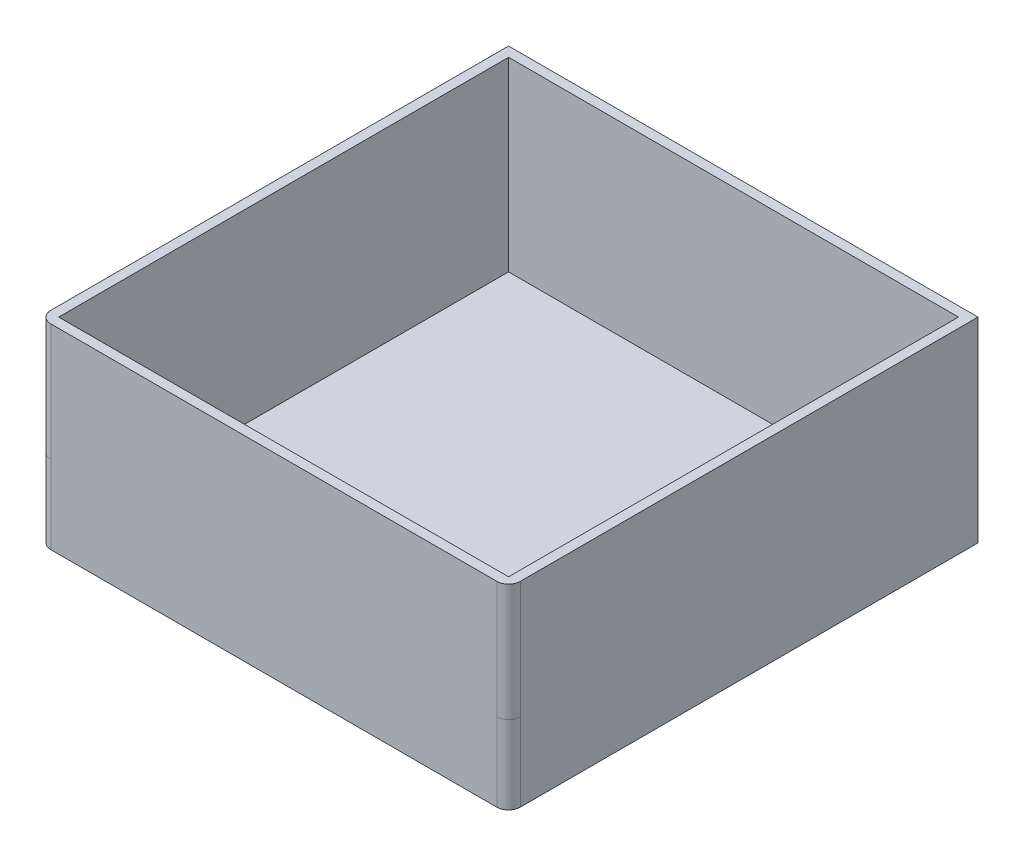
SolidWorks part; units mm, degrees
ref_plane "Plan de face" through (0, 0, 0) normal (0, 0, 1) x (1, 0, 0)
ref_plane "Plan de dessus" through (0, 0, 0) normal (0, 1, 0) x (1, 0, 0)
ref_plane "Plan de droite" through (0, 0, 0) normal (1, 0, 0) x (0, 0, -1)
sketch "Esquisse2" plane through (0, 0, 0) normal (1, 0, 0) x (0, 0, -1)
  line L0 (0, 0) -> (0, 20)
  line L1 (0, 20) -> (120, 20)
  line L2 (120, 20) -> (120, 0)
  line L3 (120, 0) -> (118.744, 0)
  line L4 (0, 0) -> (120, 0)
  dimension "D1" = 20
  dimension "D2" = 120
extrude "Boss.-Extru.1" add sketch "Esquisse2" along normal blind 120 contours L0 L4 L3 L2 L1
fillet "Congé1" radius 3 2 edges at (0, 10, 0) (120, 10, 0)
sketch "Esquisse3" plane through (0, 20, 0) normal (0, 1, 0) x (1, 0, 0)
  line L0 (0, 120) -> (120, 120) construction
  line L1 (120, 120) -> (60, 120) construction
  line L2 (60, 120) -> (60, 0) construction
  line L3 (117, 0) -> (3, 0) construction
  line L4 (60, 0) -> (60, 60) construction
  line L5 (60, 60) -> (0, 60) construction
  line L6 (0, 3) -> (0, 120) construction
  line L7 (0, 60) -> (120, 60) construction
  line L8 (120, 3) -> (120, 120) construction
  line L9 (120, 60) -> (60, 0) construction
  line L10 (60, 0) -> (0, 60) construction
  line L11 (0, 60) -> (60, 120) construction
  line L12 (60, 120) -> (120, 60) construction
  line L13 (60, 120) -> (60, 117.5) construction
  line L14 (120, 60) -> (117.5, 60) construction
  line L15 (60, 0) -> (60, 2.5) construction
  line L16 (0, 60) -> (2.5, 60) construction
  line L18 (60, 117.5) -> (117.5, 117.5)
  line L19 (60, 117.5) -> (60, 60)
  line L20 (60, 60) -> (117.5, 60)
  line L21 (117.5, 117.5) -> (117.5, 60)
  line L22 (117.5, 60) -> (60, 60)
  line L23 (117.5, 60) -> (117.5, 2.5)
  line L24 (117.5, 2.5) -> (60, 2.5)
  line L25 (60, 60) -> (60, 2.5)
  line L26 (60, 2.5) -> (2.5, 2.5)
  line L27 (60, 2.5) -> (60, 60)
  line L28 (60, 60) -> (2.5, 60)
  line L29 (2.5, 2.5) -> (2.5, 60)
  line L30 (2.5, 60) -> (60, 60)
  line L31 (2.5, 60) -> (2.5, 117.5)
  line L32 (2.5, 117.5) -> (60, 117.5)
  line L33 (60, 60) -> (60, 117.5)
  dimension "D1" = 2.5
  dimension "D2" = 2.5
  dimension "D3" = 2.5
  dimension "D4" = 2.5
extrude "Enlèv. mat.-Extru.1" cut sketch "Esquisse3" against normal blind 17.5 contours L32 L31 L28 L19 | L21 L18 L19 L20 | L29 L26 L25 L28 | L20 L25 L24 L23
sketch "Esquisse4" plane through (0, 20, 0) normal (0, 1, 0) x (1, 0, 0)
  line L1 (0, 120) -> (120, 120)
  line L2 (0, 120) -> (0, 0)
  line L3 (0, 0) -> (120, 0)
  line L4 (120, 120) -> (120, 0)
  line L5 (2.5, 117.5) -> (117.5, 117.5)
  line L6 (2.5, 117.5) -> (2.5, 2.5)
  line L7 (2.5, 2.5) -> (117.5, 2.5)
  line L8 (117.5, 117.5) -> (117.5, 2.5)
extrude "Boss.-Extru.2" add sketch "Esquisse4" along normal blind 30
fillet "Congé2" radius 3 2 edges at (120, 35, 0) (0, 35, 0)
